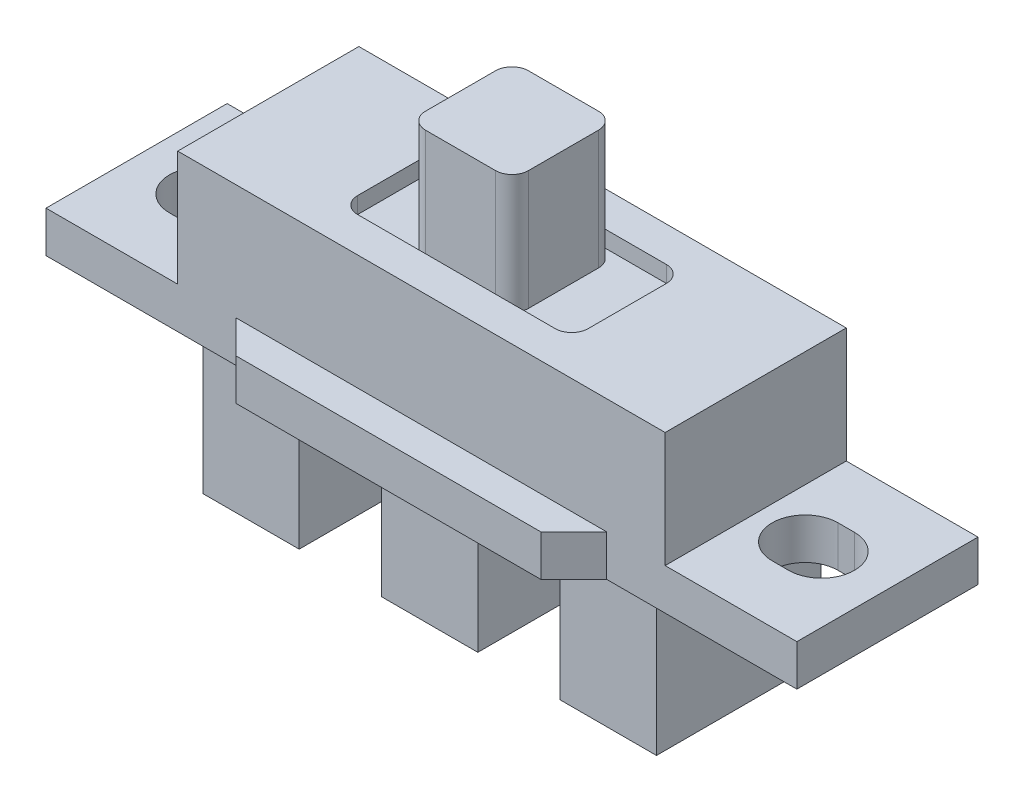
SolidWorks part; units mm, degrees
ref_plane "Front Plane" through (0, 0, 0) normal (0, 0, 1) x (1, 0, 0)
ref_plane "Top Plane" through (0, 0, 0) normal (0, 1, 0) x (1, 0, 0)
ref_plane "Right Plane" through (0, 0, 0) normal (1, 0, 0) x (0, 0, -1)
sketch "Sketch1" plane through (0, 0, 0) normal (0, 1, 0) x (1, 0, 0)
  line L1 (-14.8, -5.5) -> (14.8, -5.5)
  line L2 (-14.8, -5.5) -> (-14.8, 5.5)
  line L3 (-14.8, 5.5) -> (14.8, 5.5)
  line L4 (14.8, -5.5) -> (14.8, 5.5)
  line L5 (-14.8, -5.5) -> (14.8, 5.5) construction
  line L6 (-14.8, 5.5) -> (14.8, -5.5) construction
  point P0 (0, 0)
  dimension "D1" = 29.6
  dimension "D2" = 11
extrude "Boss-Extrude1" add sketch "Sketch1" along normal blind 7
sketch "Sketch2" plane through (0, 7, 0) normal (0, 1, 0) x (1, 0, 0)
  line L1 (-3.125, -3.125) -> (3.125, -3.125)
  line L2 (-3.125, -3.125) -> (-3.125, 3.125)
  line L3 (-3.125, 3.125) -> (3.125, 3.125)
  line L4 (3.125, -3.125) -> (3.125, 3.125)
  line L5 (-3.125, -3.125) -> (3.125, 3.125) construction
  line L6 (-3.125, 3.125) -> (3.125, -3.125) construction
  point P0 (0, 0)
  dimension "D1" = 6.25
  dimension "D2" = 6.25
extrude "Boss-Extrude2" add sketch "Sketch2" along normal blind 6.25
sketch "Sketch3" plane through (0, 0, 0) normal (0, -1, 0) x (1, 0, 0)
  line L0 (-14.8, -5.5) -> (-14.8, 5.5) construction
  line L1 (-22.8, -5.5) -> (22.8, -5.5)
  line L2 (-22.8, -5.5) -> (-22.8, 5.5)
  line L3 (-22.8, 5.5) -> (22.8, 5.5)
  line L4 (22.8, -5.5) -> (22.8, 5.5)
  line L5 (-22.8, -5.5) -> (22.8, 5.5) construction
  line L6 (-22.8, 5.5) -> (22.8, -5.5) construction
  line L7 (0, 5.5) -> (0, 7.5)
  line L8 (0, -7.15) -> (0, 7.15) construction
  line L9 (-11.25, 5.5) -> (-9.25, 7.5)
  line L10 (-9.25, 7.5) -> (0, 7.5)
  line L11 (0, 7.5) -> (9.25, 7.5)
  line L12 (9.25, 7.5) -> (11.25, 5.5)
  line L13 (7.2875, 0) -> (-7.2875, 0) construction
  line L14 (-11.25, -5.5) -> (-9.25, -7.5)
  line L15 (9.25, -7.5) -> (11.25, -5.5)
  line L16 (0, -7.5) -> (9.25, -7.5)
  line L17 (-9.25, -7.5) -> (0, -7.5)
  point P0 (0, 0)
  point P15 (0, 0)
  line M2 (14.8, -5.5) -> (14.8, 5.5)
  line M3 (14.8, 5.5) -> (-14.8, 5.5)
  line M4 (-14.8, 5.5) -> (-14.8, -5.5)
  line M5 (-14.8, -5.5) -> (14.8, -5.5)
  dimension "D1" = 8
  dimension "D2" = 8
  dimension "D3" = 2
  dimension "D4" = 45
  dimension "D5" = 45
  dimension "D6" = 22.5
extrude "Boss-Extrude3" add sketch "Sketch3" along normal blind 2.5 contours L3 L2 L1 M4 | L1 L3 M5 M2 M3 M4 | L10 L9 L3 L7 | L12 L11 L7 L3 | L1 L4 L3 M2 | L14 L17 L16 L15 L1
sketch "Sketch4" plane through (0, 0, 0) normal (0, 1, 0) x (1, 0, 0)
  line L0 (-18.8, 0) -> (-17.8, 0) construction
  line L1 (-8.6625, 0) -> (8.6625, 0) construction
  line L2 (-18.8, 2) -> (-17.8, 2)
  line L3 (-18.8, -2) -> (-17.8, -2)
  line L4 (-22.8, 5.5) -> (-22.8, -5.5) construction
  line L5 (0, -8.25) -> (0, 8.25) construction
  line L6 (18.8, 0) -> (17.8, 0) construction
  line L7 (18.8, 2) -> (17.8, 2)
  line L8 (18.8, -2) -> (17.8, -2)
  arc A0 (-18.8, 2) -> (-18.8, -2) centre (-18.8, 0) ccw
  arc A1 (-17.8, -2) -> (-17.8, 2) centre (-17.8, 0) ccw
  arc A2 (18.8, 2) -> (18.8, -2) centre (18.8, 0) cw
  arc A3 (17.8, -2) -> (17.8, 2) centre (17.8, 0) cw
  point P5 (-18.3, 0)
  point P12 (0, 0)
  point P13 (0, 0)
  point P18 (18.3, 0)
  dimension "D1" = 4
  dimension "D2" = 4
  dimension "D3" = 1
extrude "Cut-Extrude1" cut sketch "Sketch4" against normal through all both and the other way through all
sketch "Sketch5" plane through (0, -2.5, 0) normal (0, -1, 0) x (1, 0, 0)
  line L0 (8.6625, 0) -> (-8.6625, 0) construction
  line L1 (-2.925, -5) -> (2.925, -5)
  line L2 (-2.925, -5) -> (-2.925, 5)
  line L3 (-2.925, 5) -> (2.925, 5)
  line L4 (2.925, -5) -> (2.925, 5)
  line L5 (-2.925, -5) -> (2.925, 5) construction
  line L6 (-2.925, 5) -> (2.925, -5) construction
  line L7 (7.925, -5) -> (13.775, -5)
  line L8 (7.925, -5) -> (7.925, 5)
  line L9 (7.925, 5) -> (13.775, 5)
  line L10 (13.775, -5) -> (13.775, 5)
  line L11 (7.925, -5) -> (13.775, 5) construction
  line L12 (7.925, 5) -> (13.775, -5) construction
  line L13 (0, -8.25) -> (0, 8.25) construction
  line L14 (-7.925, 5) -> (-13.775, 5)
  line L15 (-13.775, -5) -> (-13.775, 5)
  line L16 (-7.925, -5) -> (-13.775, -5)
  line L17 (-7.925, -5) -> (-7.925, 5)
  point P0 (0, 0)
  point P6 (10.85, 0)
  dimension "D1" = 5.85
  dimension "D2" = 10
  dimension "D3" = 5
extrude "Boss-Extrude4" add sketch "Sketch5" along normal blind 8.25
sketch "Sketch6" plane through (0, -10.75, 0) normal (0, -1, 0) x (1, 0, 0)
  line L0 (0, -5) -> (0, -3)
  line L1 (-2.925, -5) -> (2.925, -5) construction
  line L2 (0, -8.25) -> (0, 8.25) construction
  line L3 (-2, -3) -> (2, -3)
  line L4 (8.85, -3) -> (12.85, -3)
  line L5 (-12.85, -3) -> (-8.85, -3)
  arc A0 (2, -3) -> (-2, -3) centre (0, -3) ccw
  arc A1 (-2, -3) -> (0, -5) centre (0, -3) ccw construction
  arc A2 (0, -5) -> (2, -3) centre (0, -3) ccw construction
  arc A3 (12.85, -3) -> (8.85, -3) centre (10.85, -3) ccw
  arc A4 (-8.85, -3) -> (-12.85, -3) centre (-10.85, -3) ccw
  dimension "D2" = 2
  dimension "D1" = 2
  dimension "D3" = 2
extrude "Cut-Extrude2" cut sketch "Sketch6" against normal blind 3 contours L3 A0 | L4 A3 | L5 A4
sketch "Sketch7" plane through (0, 7, 0) normal (0, 1, 0) x (1, 0, 0)
  line L1 (-7, -3.375) -> (7, -3.375)
  line L2 (-7, -3.375) -> (-7, 3.375)
  line L3 (-7, 3.375) -> (7, 3.375)
  line L4 (7, -3.375) -> (7, 3.375)
  line L5 (-7, -3.375) -> (7, 3.375) construction
  line L6 (-7, 3.375) -> (7, -3.375) construction
  point P0 (0, 0)
  line M7 (3.125, 3.125) -> (3.125, -3.125)
  line M8 (3.125, -3.125) -> (-3.125, -3.125)
  line M9 (-3.125, -3.125) -> (-3.125, 3.125)
  line M10 (-3.125, 3.125) -> (3.125, 3.125)
  dimension "D1" = 6.75
  dimension "D2" = 14
extrude "Cut-Extrude3" cut sketch "Sketch7" against normal blind 1 contours L1 L4 L3 L2 M10 M7 M8 M9
fillet "Fillet1" radius 1 4 edges at (-7, 6.5, 3.375) (-7, 6.5, -3.375) (7, 6.5, 3.375) (7, 6.5, -3.375)
fillet "Fillet2" radius 1 4 edges at (-3.125, 9.625, 3.125) (-3.125, 9.625, -3.125) (3.125, 9.625, -3.125) (3.125, 9.625, 3.125)
